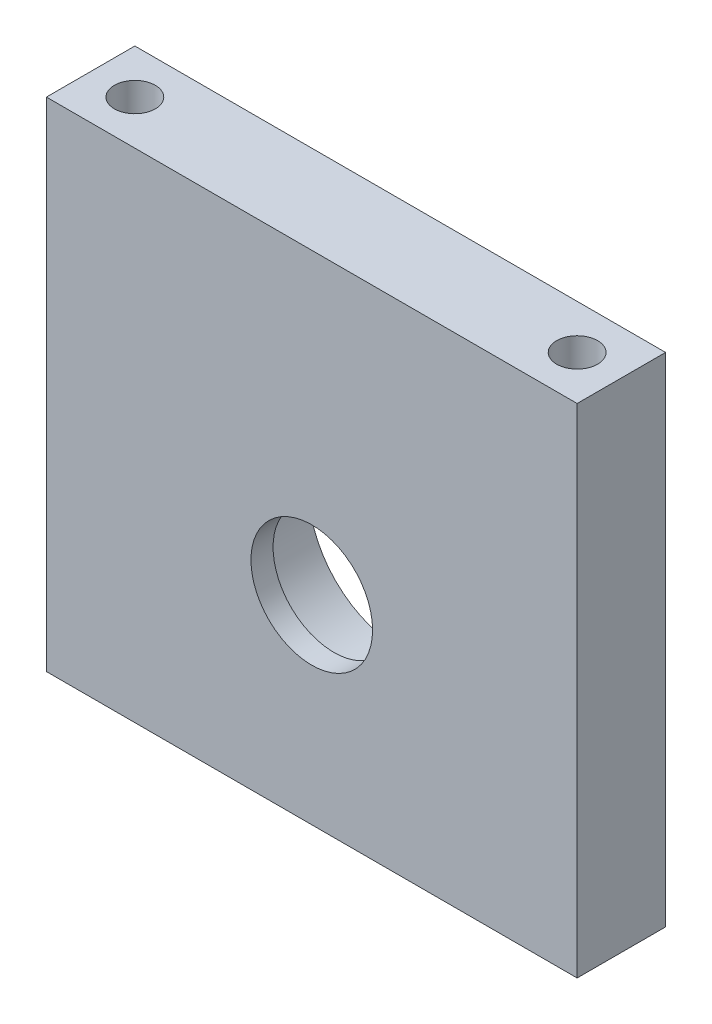
SolidWorks part; units mm, degrees
material "Alliage 1060"
ref_plane "Plan de face" through (0, 0, 0) normal (0, 0, 1) x (1, 0, 0)
ref_plane "Plan de dessus" through (0, 0, 0) normal (0, 1, 0) x (1, 0, 0)
ref_plane "Plan de droite" through (0, 0, 0) normal (1, 0, 0) x (0, 0, -1)
sketch "Esquisse1" plane through (0, 0, 0) normal (0, 0, 1) x (1, 0, 0)
  line L1 (-24, 22.5) -> (24, 22.5)
  line L2 (-24, 22.5) -> (-24, -22.5)
  line L3 (-24, -22.5) -> (24, -22.5)
  line L4 (24, 22.5) -> (24, -22.5)
  line L5 (-24, 22.5) -> (24, -22.5) construction
  line L6 (-24, -22.5) -> (24, 22.5) construction
  point P0 (0, 0)
  dimension "D1" = 45
  dimension "D2" = 48
extrude "Boss.-Extru.1" add sketch "Esquisse1" along normal blind 8
sketch "Esquisse2" plane through (0, -22.5, 0) normal (0, -1, 0) x (1, 0, 0)
  line L1 (21.75, 4) -> (24, 4) construction
  line L2 (-24, 4) -> (-21.75, 4) construction
  line L3 (-24, 8) -> (-24, 0) construction
  line L4 (24, 8) -> (24, 0) construction
  line L5 (-20, 5.75) -> (-20, 8) construction
  line L6 (-24, 8) -> (24, 8) construction
  line L7 (-21.75, 4) -> (-24, 4) construction
  line L8 (21.75, 4) -> (24, 4) construction
  circle A0 centre (-20, 4) radius 1.75
  circle A1 centre (20, 4) radius 1.75
  dimension "D1" = 3.5
  dimension "D2" = 3.5
  dimension "D3" = 40
sketch "Esquisse3" plane through (0, 22.5, 0) normal (0, 1, 0) x (1, 0, 0)
  line L1 (-24, -8) -> (-24, 0) construction
  line L2 (24, -8) -> (24, 0) construction
  line L3 (-21.75, -4) -> (-24, -4) construction
  line L4 (21.75, -4) -> (24, -4) construction
  circle A0 centre (-20, -4) radius 1.75
  circle A1 centre (20, -4) radius 1.75
  dimension "D3" = 3.5
  dimension "D4" = 3.5
  dimension "D1" = 40
sketch "Esquisse4" plane through (0, 0, 0) normal (0, 0, -1) x (-1, 0, 0)
  line L0 (24, -22.5) -> (-24, -22.5) construction
  line L1 (0, 22.5) -> (0, -22.5) construction
  line L2 (-24, 22.5) -> (24, 22.5) construction
  circle A0 centre (0, -4.5) radius 8.25
  dimension "D1" = 18
  dimension "D2" = 16.5
sketch "Esquisse5" plane through (0, 0, 8) normal (0, 0, 1) x (1, 0, 0)
  circle A0 centre (0, -4.5) radius 5.5
  dimension "D1" = 11
extrude "Enlèv. mat.-Extru.3" cut sketch "Esquisse5" against normal blind 2
extrude "Enlèv. mat.-Extru.4" cut sketch "Esquisse4" against normal blind 6
extrude "Enlèv. mat.-Extru.5" cut sketch "Esquisse2" against normal blind 10
hole_wizard "Dégagement M3.51" positions "Esquisse3D1" profile "Esquisse6" hole size "M3.5" standard "ISO"
sketch3d "Esquisse3D1"
  point P0 (20, 22.5, 4)
  point P3 (-20, 22.5, 4)
  point P6 (-58.3612, 70.8597, 0)
  point P8 (-58.3612, 70.8597, 0)
sketch "Esquisse6" plane through (20, 22.5, 4) normal (1, 0, 0) x (0, 0, 1)
  line L0 (0, 0) -> (0, 11.1116)
  line L1 (0, 11.1116) -> (1.85, 10)
  line L2 (1.85, 10) -> (1.85, 0)
  line L5 (1.85, 0) -> (0, 0)
  line L10 (0, 11.1116) -> (-1.85, 10) construction
  line L11 (0, -6.35) -> (0, 107.95) construction
  dimension "Diamètre du perçage" = 3.7
  dimension "Profondeur du perçage" = 10
  dimension "Angle de pointe" = 118
